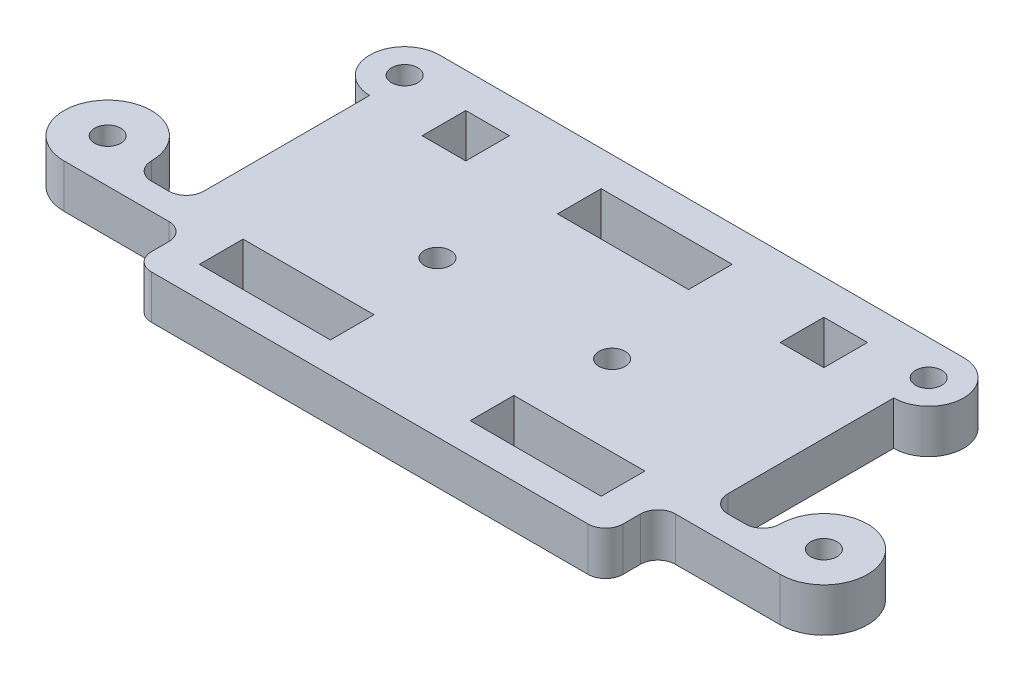
SolidWorks part; units mm, degrees
ref_plane "Front Plane" through (0, 0, 0) normal (0, 0, 1) x (1, 0, 0)
ref_plane "Top Plane" through (0, 0, 0) normal (0, 1, 0) x (1, 0, 0)
ref_plane "Right Plane" through (0, 0, 0) normal (1, 0, 0) x (0, 0, -1)
sketch "Sketch1" plane through (0, 0, 0) normal (0, 1, 0) x (1, 0, 0)
  line L0 (-29, -11.75) -> (-30, -11.75)
  line L2 (-30, -6.75) -> (-30, 12.25)
  line L3 (-30, 20.25) -> (30, 20.25)
  line L4 (30, -6.75) -> (30, 12.25)
  line L5 (0, 20.25) -> (0, -17.75) construction
  line L6 (-30, 0) -> (30, 0) construction
  line L7 (-29, -11.75) -> (-29, -13.75) construction
  line L8 (-23, 16.25) -> (-18, 16.25)
  line L9 (-23, 16.25) -> (-23, 11.25)
  line L10 (-23, 11.25) -> (-18, 11.25)
  line L11 (-18, 16.25) -> (-18, 11.25)
  line L12 (-20.5, 11.25) -> (-20.5, 16.25) construction
  line L13 (-23, 13.75) -> (-18, 13.75) construction
  line L14 (-7.5, 16.25) -> (7.5, 16.25)
  line L15 (-7.5, 16.25) -> (-7.5, 11.25)
  line L16 (-7.5, 11.25) -> (7.5, 11.25)
  line L17 (7.5, 16.25) -> (7.5, 11.25)
  line L18 (0, 11.25) -> (0, 16.25) construction
  line L19 (-7.5, 13.75) -> (7.5, 13.75) construction
  line L20 (18, 16.25) -> (23, 16.25)
  line L21 (18, 16.25) -> (18, 11.25)
  line L22 (18, 11.25) -> (23, 11.25)
  line L23 (23, 16.25) -> (23, 11.25)
  line L24 (20.5, 11.25) -> (20.5, 16.25) construction
  line L25 (18, 13.75) -> (23, 13.75) construction
  line L26 (-23, -9.25) -> (-8, -9.25)
  line L27 (-23, -9.25) -> (-23, -14.25)
  line L28 (-23, -14.25) -> (-8, -14.25)
  line L29 (-8, -9.25) -> (-8, -14.25)
  line L30 (-29, -13.75) -> (-27, -13.75) construction
  line L31 (-25, -17.75) -> (25, -17.75)
  line L32 (8, -9.25) -> (23, -9.25)
  line L33 (8, -9.25) -> (8, -14.25)
  line L34 (8, -14.25) -> (23, -14.25)
  line L35 (23, -9.25) -> (23, -14.25)
  line L37 (29, -11.75) -> (30, -11.75)
  line L38 (-30, -11.75) -> (-41, -11.75)
  line L39 (-27, -13.75) -> (-27, -15.75)
  line L40 (27, -13.75) -> (27, -15.75)
  line L41 (30, -11.75) -> (41, -11.75)
  line L42 (-34, -6.75) -> (-36, -6.75) construction
  line L43 (-34, -6.75) -> (-34, -8.75) construction
  line L44 (32, -8.75) -> (34, -8.75)
  line L45 (-32, -6.75) -> (-32, -8.75) construction
  line L46 (-32, -6.75) -> (-30, -6.75) construction
  line L47 (-34, -8.75) -> (-32, -8.75)
  line L48 (25, -15.75) -> (25, -17.75) construction
  line L49 (25, -15.75) -> (27, -15.75) construction
  line L50 (29, -11.75) -> (29, -13.75) construction
  line L51 (29, -13.75) -> (27, -13.75) construction
  circle A0 centre (-10, 0) radius 1.5
  circle A1 centre (10, 0) radius 1.5
  arc A2 (-30, 20.25) -> (-30, 12.25) centre (-30, 16.25) ccw
  arc A3 (30, 12.25) -> (30, 20.25) centre (30, 16.25) ccw
  circle A4 centre (-30, 16.25) radius 1.5
  circle A5 centre (30, 16.25) radius 1.5
  arc A6 (-27, -13.75) -> (-29, -11.75) centre (-29, -13.75) ccw
  arc A7 (29, -11.75) -> (27, -13.75) centre (29, -13.75) ccw
  arc A8 (25, -17.75) -> (27, -15.75) centre (25, -15.75) ccw
  arc A9 (34, -8.75) -> (36, -6.75) centre (34, -6.75) ccw
  arc A10 (-36, -6.75) -> (-34, -8.75) centre (-34, -6.75) ccw
  arc A11 (-32, -8.75) -> (-30, -6.75) centre (-32, -6.75) ccw
  arc A12 (-27, -15.75) -> (-25, -17.75) centre (-25, -15.75) ccw
  arc A13 (30, -6.75) -> (32, -8.75) centre (32, -6.75) ccw
  circle A14 centre (41, -6.75) radius 1.5
  arc A15 (41, -11.75) -> (36, -6.75) centre (41, -6.75) ccw
  arc A16 (-36, -6.75) -> (-41, -11.75) centre (-41, -6.75) ccw
  circle A17 centre (-41, -6.75) radius 1.5
  point P84 (0, 13.75)
  point P85 (20.5, 13.75)
  point P104 (0, 0)
  point P112 (-20.5, 13.75)
  dimension "D3" = 3
  dimension "D4" = 3
  dimension "D8" = 8
  dimension "D9" = 8
  dimension "D10" = 3
  dimension "D11" = 3
  dimension "D12" = 5
  dimension "D28" = 4
  dimension "D29" = 2
  dimension "D30" = 2
  dimension "D31" = 4
  dimension "D32" = 2
  dimension "D33" = 2
  dimension "D34" = 4
  dimension "D35" = 4
  dimension "D38" = 11
  dimension "D40" = 3
  dimension "D41" = 10
  dimension "D42" = 3.5
  dimension "D47" = 38
  dimension "D52" = 3
  dimension "D53" = 10
  dimension "D54" = 41
  dimension "D55" = 2
  dimension "D5" = 10
  dimension "D6" = 10
  dimension "D7" = 8
  dimension "D13" = 16.25
  dimension "D14" = 15
  dimension "D15" = 5
  dimension "D16" = 5
  dimension "D17" = 4
  dimension "D18" = 4
  dimension "D19" = 4
  dimension "D20" = 7
  dimension "D21" = 7
  dimension "D22" = 5
  dimension "D23" = 15
  dimension "D24" = 5
  dimension "D25" = 15
  dimension "D26" = 7
  dimension "D27" = 7
  dimension "D36" = 1
  dimension "D37" = 1
  dimension "D39" = 2
  dimension "D43" = 2
  dimension "D44" = 41
  dimension "D45" = 6.75
  dimension "D46" = 3.5
  dimension "D48" = 2
  dimension "D49" = 9.25
  dimension "D50" = 4
  dimension "D51" = 11
  dimension "D56" = 11.25
extrude "Boss-Extrude1" add sketch "Sketch1" along normal blind 5
